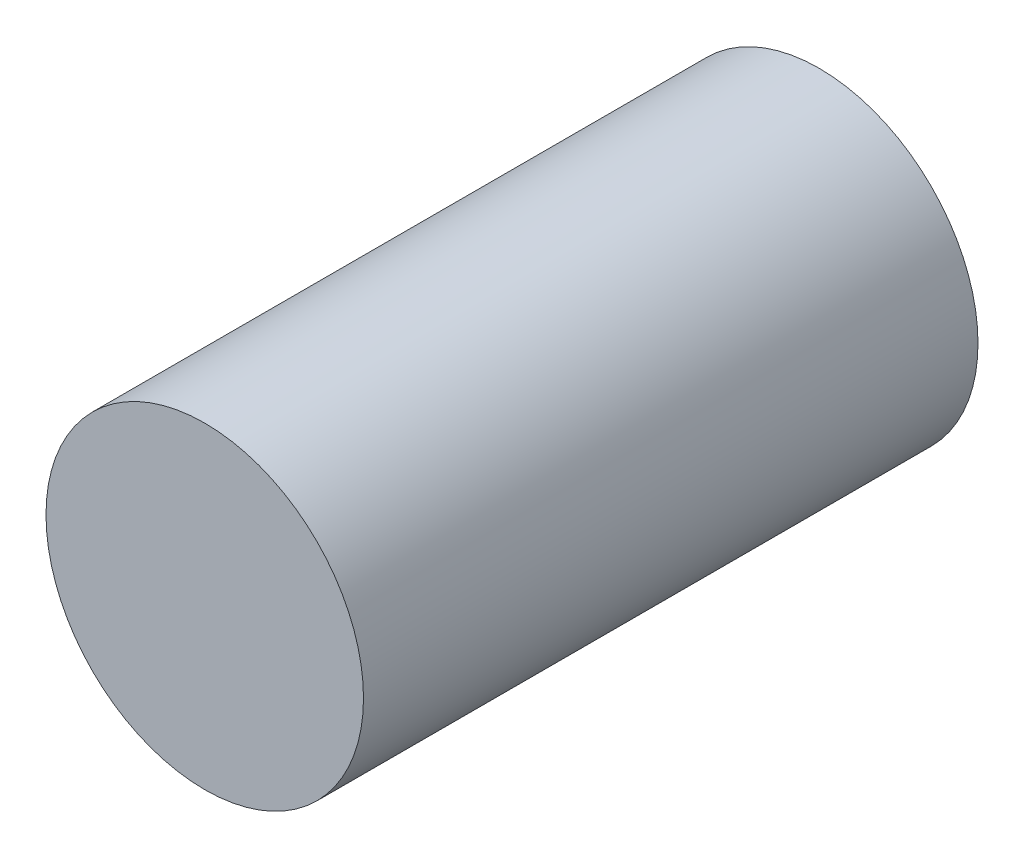
SolidWorks part; units mm, degrees
ref_plane "Alzado" through (0, 0, 0) normal (0, 0, 1) x (1, 0, 0)
ref_plane "Planta" through (0, 0, 0) normal (0, 1, 0) x (1, 0, 0)
ref_plane "Vista lateral" through (0, 0, 0) normal (1, 0, 0) x (0, 0, -1)
sketch "Croquis1" plane through (0, 0, 0) normal (0, 0, 1) x (1, 0, 0)
  circle A0 centre (0, 0) radius 1.55
  dimension "D1" = 3.1
extrude "Saliente-Extruir1" add sketch "Croquis1" along normal blind 6
